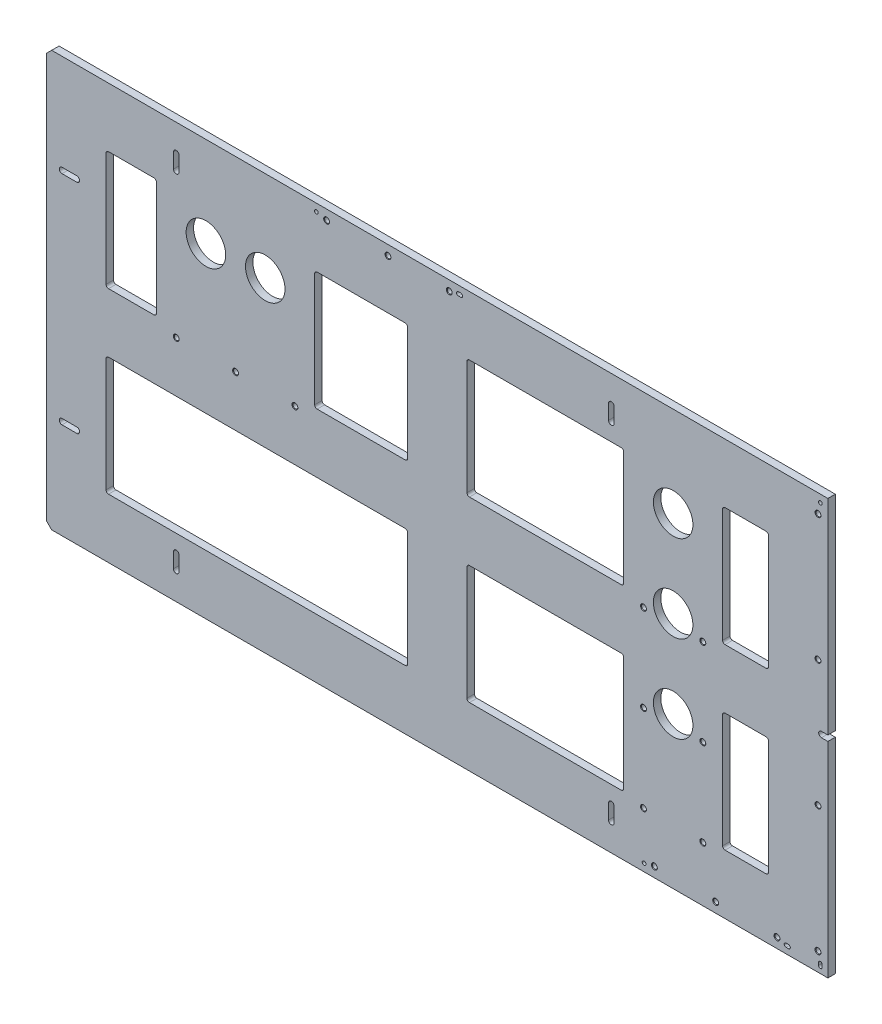
SolidWorks part; units mm, degrees
material "6061-T6 Al"
ref_plane "Front Plane" through (0, 0, 0) normal (0, 0, 1) x (1, 0, 0)
ref_plane "Top Plane" through (0, 0, 0) normal (0, 1, 0) x (1, 0, 0)
ref_plane "Right Plane" through (0, 0, 0) normal (1, 0, 0) x (0, 0, -1)
sketch "Sketch6" plane through (0, 0, 0) normal (0, 0, 1) x (1, 0, 0)
  line L0 (-1.27, -385.7625) -> (-1.27, -122.6312)
  line L1 (-13.0937, -119.0625) -> (-4.8387, -119.0625) construction
  line L2 (-80.645, -309.5625) -> (-80.645, -385.7625) construction
  line L3 (-928.37, -306.3875) -> (-1004.57, -306.3875) construction
  line L4 (0, 498.475) -> (0, -498.475) construction
  line L5 (-998.22, 147.6375) -> (-1.27, 147.6375)
  line L6 (-200, -79.8576) -> (-200, -135.6614) construction
  line L7 (-1004.57, -379.4125) -> (-1004.57, 141.2875)
  line L8 (-1.27, -385.7625) -> (-998.22, -385.7625)
  line L9 (-200, -135.6614) -> (-200, -191.4652) construction
  line L13 (-1004.57, -119.0625) -> (-483.87, -119.0625) construction
  line L15 (-1.27, -385.7625) -> (1.27, -385.7625) construction
  line L36 (-834.6313, 112.7125) -> (-834.6313, 93.6625)
  line L37 (-841.7687, 112.7125) -> (-841.7687, 93.6625)
  line L38 (-275.8313, 112.7125) -> (-275.8313, 93.6625)
  line L39 (-282.9687, 93.6625) -> (-282.9687, 112.7125)
  line L40 (-282.9687, -331.7875) -> (-282.9687, -350.8375)
  line L41 (-275.8313, -350.8375) -> (-275.8313, -331.7875)
  line L42 (-841.7687, -350.8375) -> (-841.7687, -331.7875)
  line L43 (-834.6313, -350.8375) -> (-834.6313, -331.7875)
  line L44 (-838.2, 112.7125) -> (-838.2, 103.1875) construction
  line L45 (-838.2, 103.1875) -> (-838.2, 93.6625) construction
  line L46 (-838.2, -350.8375) -> (-838.2, -341.3125) construction
  line L47 (-838.2, -341.3125) -> (-838.2, -331.7875) construction
  line L48 (-984.885, -255.1938) -> (-965.835, -255.1938)
  line L49 (-984.885, -262.3312) -> (-965.835, -262.3312)
  line L50 (-984.885, 24.2062) -> (-965.835, 24.2062)
  line L51 (-984.885, 17.0688) -> (-965.835, 17.0688)
  line L60 (-1004.57, 141.2875) -> (-998.22, 147.6375)
  line L61 (-998.22, -385.7625) -> (-1004.57, -379.4125)
  line L66 (-984.885, -255.1938) -> (-975.36, -258.7625) construction
  line L67 (-975.36, -258.7625) -> (-965.835, -262.3312) construction
  line L68 (-200, -79.8576) -> (-200, -24.0538) construction
  line L70 (-133.325, 71.4375) -> (-80.645, 71.4375)
  line L71 (-136.5, 68.2625) -> (-136.5, -77.7875)
  line L72 (-133.325, -309.5625) -> (-80.645, -309.5625)
  line L74 (-77.47, 68.2625) -> (-77.47, -77.7875)
  line L75 (-80.645, 71.4375) -> (-80.645, 147.6375) construction
  line L76 (-263.5, 68.2625) -> (-263.5, -77.7875)
  line L77 (-136.5, -160.3375) -> (-136.5, -306.3875)
  line L78 (-263.5, -160.3375) -> (-263.5, -306.3875)
  line L79 (-1.27, 147.6375) -> (-1004.57, -385.7625) construction
  line L80 (-502.92, 68.2625) -> (-502.92, -119.0625) construction
  line L81 (-266.675, 71.4375) -> (-461.645, 71.4375)
  line L82 (-660.4, 68.2625) -> (-660.4, -77.7875)
  line L83 (-266.675, -157.1625) -> (-461.645, -157.1625)
  line L86 (-657.225, -80.9625) -> (-544.195, -80.9625)
  line L87 (-266.675, -309.5625) -> (-461.645, -309.5625)
  line L88 (-464.82, 68.2625) -> (-464.82, -77.7875)
  line L89 (-464.82, -160.3375) -> (-464.82, -306.3875)
  line L90 (-928.37, -160.3375) -> (-928.37, -306.3875)
  line L91 (-77.47, 68.2625) -> (-1.27, 68.2625) construction
  line L92 (-541.02, -160.3375) -> (-541.02, -306.3875)
  line L93 (-541.02, 68.2625) -> (-541.02, -77.7875)
  line L94 (-544.195, 71.4375) -> (-657.225, 71.4375)
  line L95 (-461.645, -80.9625) -> (-266.675, -80.9625)
  line L96 (-544.195, -157.1625) -> (-925.195, -157.1625)
  line L97 (-544.195, -309.5625) -> (-925.195, -309.5625)
  line L98 (-541.02, 68.2625) -> (-464.82, 68.2625) construction
  line L165 (-800.1, 31.75) -> (-723.9, 31.75) construction
  line L166 (-762, 31.75) -> (-762, -80.9625) construction
  line L168 (-925.195, 71.4375) -> (-866.775, 71.4375)
  line L169 (-928.37, 68.2625) -> (-928.37, -77.7875)
  line L170 (-925.195, -80.9625) -> (-866.775, -80.9625)
  line L171 (-863.6, 68.2625) -> (-863.6, -77.7875)
  line L178 (-502.92, -119.0625) -> (-502.92, -385.7625) construction
  line L180 (-133.325, -80.9625) -> (-80.645, -80.9625)
  line L181 (-133.325, -157.1625) -> (-80.645, -157.1625)
  line L182 (-77.47, -160.3375) -> (-77.47, -306.3875)
  line L186 (-200, -24.0538) -> (-200, 31.75) construction
  line L187 (-241.275, -223.2152) -> (-158.725, -223.2152) construction
  line L188 (-244.45, -226.3902) -> (-244.45, -306.3875) construction
  line L189 (-241.275, -309.5625) -> (-158.725, -309.5625) construction
  line L190 (-155.55, -226.3902) -> (-155.55, -306.3875) construction
  line L191 (-155.55, -24.0538) -> (-155.55, -44.9326) construction
  line L195 (-241.275, 0) -> (-158.725, 0) construction
  line L196 (-244.45, -3.175) -> (-244.45, -44.9326) construction
  line L197 (-241.275, -48.1076) -> (-158.725, -48.1076) construction
  line L198 (-155.55, -3.175) -> (-155.55, -24.0538) construction
  line L206 (-841.375, 0) -> (-790.575, 0) construction
  line L207 (-844.55, -3.175) -> (-844.55, -77.7875) construction
  line L208 (-841.375, -80.9625) -> (-790.575, -80.9625) construction
  line L209 (-787.4, -3.175) -> (-787.4, -77.7875) construction
  line L210 (-736.6, -3.175) -> (-736.6, -77.7875) construction
  line L211 (-682.625, -80.9625) -> (-733.425, -80.9625) construction
  line L212 (-679.45, -3.175) -> (-679.45, -77.7875) construction
  line L214 (-682.625, 0) -> (-733.425, 0) construction
  line L228 (-1.27, -122.6312) -> (-9.525, -122.6312)
  line L229 (-1.27, -115.4938) -> (-9.525, -115.4938)
  line L230 (-1.27, -115.4938) -> (-1.27, 147.6375)
  circle A5 centre (-723.9, 31.75) radius 25.4
  circle A6 centre (-800.1, 31.75) radius 25.4
  circle A10 centre (-200, -191.4652) radius 25.4
  circle A11 centre (-200, -79.8576) radius 25.4
  circle A12 centre (-200, 31.75) radius 25.4
  arc A17 (-834.6313, 93.6625) -> (-841.7687, 93.6625) centre (-838.2, 93.6625) cw
  arc A18 (-841.7687, 112.7125) -> (-834.6313, 112.7125) centre (-838.2, 112.7125) cw
  arc A19 (-275.8313, 93.6625) -> (-282.9687, 93.6625) centre (-279.4, 93.6625) cw
  arc A20 (-275.8313, 112.7125) -> (-282.9687, 112.7125) centre (-279.4, 112.7125) ccw
  arc A21 (-275.8313, -350.8375) -> (-282.9687, -350.8375) centre (-279.4, -350.8375) cw
  arc A22 (-275.8313, -331.7875) -> (-282.9687, -331.7875) centre (-279.4, -331.7875) ccw
  arc A23 (-841.7687, -350.8375) -> (-834.6313, -350.8375) centre (-838.2, -350.8375) ccw
  arc A24 (-834.6313, -331.7875) -> (-841.7687, -331.7875) centre (-838.2, -331.7875) ccw
  arc A25 (-984.885, -262.3312) -> (-984.885, -255.1938) centre (-984.885, -258.7625) cw
  arc A26 (-965.835, -255.1938) -> (-965.835, -262.3312) centre (-965.835, -258.7625) cw
  arc A31 (-965.835, 17.0688) -> (-965.835, 24.2062) centre (-965.835, 20.6375) ccw
  arc A32 (-984.885, 24.2062) -> (-984.885, 17.0688) centre (-984.885, 20.6375) ccw
  arc A41 (-925.195, -157.1625) -> (-928.37, -160.3375) centre (-925.195, -160.3375) ccw
  arc A42 (-928.37, -306.3875) -> (-925.195, -309.5625) centre (-925.195, -306.3875) ccw
  arc A43 (-541.02, -306.3875) -> (-544.195, -309.5625) centre (-544.195, -306.3875) cw
  arc A44 (-541.02, -160.3375) -> (-544.195, -157.1625) centre (-544.195, -160.3375) ccw
  arc A45 (-657.225, 71.4375) -> (-660.4, 68.2625) centre (-657.225, 68.2625) ccw
  arc A46 (-657.225, -80.9625) -> (-660.4, -77.7875) centre (-657.225, -77.7875) cw
  arc A47 (-541.02, -77.7875) -> (-544.195, -80.9625) centre (-544.195, -77.7875) cw
  arc A48 (-541.02, 68.2625) -> (-544.195, 71.4375) centre (-544.195, 68.2625) ccw
  arc A49 (-263.5, 68.2625) -> (-266.675, 71.4375) centre (-266.675, 68.2625) ccw
  arc A50 (-464.82, 68.2625) -> (-461.645, 71.4375) centre (-461.645, 68.2625) cw
  arc A51 (-464.82, -77.7875) -> (-461.645, -80.9625) centre (-461.645, -77.7875) ccw
  arc A52 (-263.5, -77.7875) -> (-266.675, -80.9625) centre (-266.675, -77.7875) cw
  arc A53 (-266.675, -157.1625) -> (-263.5, -160.3375) centre (-266.675, -160.3375) cw
  arc A54 (-464.82, -160.3375) -> (-461.645, -157.1625) centre (-461.645, -160.3375) cw
  arc A55 (-461.645, -309.5625) -> (-464.82, -306.3875) centre (-461.645, -306.3875) cw
  arc A56 (-266.675, -309.5625) -> (-263.5, -306.3875) centre (-266.675, -306.3875) ccw
  arc A57 (-136.5, -306.3875) -> (-133.325, -309.5625) centre (-133.325, -306.3875) ccw
  arc A58 (-80.645, -309.5625) -> (-77.47, -306.3875) centre (-80.645, -306.3875) ccw
  arc A59 (-80.645, 71.4375) -> (-77.47, 68.2625) centre (-80.645, 68.2625) cw
  arc A60 (-133.325, 71.4375) -> (-136.5, 68.2625) centre (-133.325, 68.2625) ccw
  arc A81 (-866.775, -80.9625) -> (-863.6, -77.7875) centre (-866.775, -77.7875) ccw
  arc A93 (-928.37, -77.7875) -> (-925.195, -80.9625) centre (-925.195, -77.7875) ccw
  arc A95 (-866.775, 71.4375) -> (-863.6, 68.2625) centre (-866.775, 68.2625) cw
  arc A96 (-925.195, 71.4375) -> (-928.37, 68.2625) centre (-925.195, 68.2625) ccw
  arc A101 (-133.325, -157.1625) -> (-136.5, -160.3375) centre (-133.325, -160.3375) ccw
  arc A102 (-80.645, -157.1625) -> (-77.47, -160.3375) centre (-80.645, -160.3375) cw
  arc A103 (-80.645, -80.9625) -> (-77.47, -77.7875) centre (-80.645, -77.7875) ccw
  arc A104 (-136.5, -77.7875) -> (-133.325, -80.9625) centre (-133.325, -77.7875) ccw
  arc A109 (-158.725, -48.1076) -> (-155.55, -44.9326) centre (-158.725, -44.9326) ccw construction
  arc A110 (-158.725, 0) -> (-155.55, -3.175) centre (-158.725, -3.175) cw construction
  arc A111 (-241.275, 0) -> (-244.45, -3.175) centre (-241.275, -3.175) ccw construction
  arc A112 (-244.45, -44.9326) -> (-241.275, -48.1076) centre (-241.275, -44.9326) ccw construction
  arc A117 (-158.725, -309.5625) -> (-155.55, -306.3875) centre (-158.725, -306.3875) ccw construction
  arc A118 (-158.725, -223.2152) -> (-155.55, -226.3902) centre (-158.725, -226.3902) cw construction
  arc A119 (-241.275, -223.2152) -> (-244.45, -226.3902) centre (-241.275, -226.3902) ccw construction
  arc A120 (-244.45, -306.3875) -> (-241.275, -309.5625) centre (-241.275, -306.3875) ccw construction
  arc A125 (-679.45, -77.7875) -> (-682.625, -80.9625) centre (-682.625, -77.7875) cw construction
  arc A126 (-682.625, 0) -> (-679.45, -3.175) centre (-682.625, -3.175) cw construction
  arc A127 (-733.425, 0) -> (-736.6, -3.175) centre (-733.425, -3.175) ccw construction
  arc A128 (-733.425, -80.9625) -> (-736.6, -77.7875) centre (-733.425, -77.7875) cw construction
  arc A129 (-790.575, -80.9625) -> (-787.4, -77.7875) centre (-790.575, -77.7875) ccw construction
  arc A130 (-790.575, 0) -> (-787.4, -3.175) centre (-790.575, -3.175) cw construction
  arc A131 (-841.375, 0) -> (-844.55, -3.175) centre (-841.375, -3.175) ccw construction
  arc A132 (-844.55, -77.7875) -> (-841.375, -80.9625) centre (-841.375, -77.7875) ccw construction
  arc A141 (-9.525, -122.6312) -> (-9.525, -115.4938) centre (-9.525, -119.0625) cw
  dimension "D2" = 533.4
  dimension "D5" = 147.6375
  dimension "D6" = 203.2
  dimension "D7" = 2.54
  dimension "D9" = 9.525
  dimension "D12" = 975.36
  dimension "D11" = 3.175
  dimension "D13" = 200
  dimension "D14" = 50.8
  dimension "D16" = 223.2152
  dimension "D19" = 7.1374
  dimension "D20" = 444.5
  dimension "D22" = 558.8
  dimension "D23" = 279.4
  dimension "D21" = 279.4
  dimension "D34" = 63.5
  dimension "D17" = 31.75
  dimension "D44" = 88.9
  dimension "D49" = 19.05
  dimension "D47" = 63.5
  dimension "D8" = 1004.57
  dimension "D15" = 762
  dimension "D18" = 19.05
  dimension "D29" = 76.2
  dimension "D30" = 127
  dimension "D33" = 76.2
  dimension "D45" = 6.35
  dimension "D46" = 6.35
  dimension "D48" = 6.35
extrude "Boss-Extrude1" add sketch "Sketch6" against normal mid plane 9.525
hole_wizard "1/4-20 Tapped Hole1" positions "Sketch8" profile "Sketch7" tap size "1/4-20" standard "ANSI Inch" end condition through all
sketch "Sketch8" plane through (0, 0, 4.7625) normal (0, 0, 1) x (1, 0, 0)
  line L0 (-762, -92.075) -> (-723.9, 31.75) construction
  line L1 (-762, -92.075) -> (-800.1, 31.75) construction
  line L2 (-762, -92.075) -> (-800.1, -92.075) construction
  line L3 (-762, -92.075) -> (-723.9, -92.075) construction
  line L6 (-238.1, -92.075) -> (-238.1, -203.6826) construction
  line L7 (-238.1, -203.6826) -> (-238.1, -315.2902) construction
  line L10 (-238.1, -92.075) -> (-200, -92.075) construction
  line L11 (-200, -79.8576) -> (-200, 31.75) construction
  line L12 (-200, -92.075) -> (-161.9, -92.075) construction
  line L13 (-238.1, -203.6826) -> (-200, -203.6826) construction
  line L14 (-238.1, -315.2902) -> (-200, -315.2902) construction
  line L15 (-200, -203.6826) -> (-161.9, -203.6826) construction
  line L16 (-200, -315.2902) -> (-161.9, -315.2902) construction
  line L17 (-800.1, -92.075) -> (-838.2, -92.075) construction
  line L18 (-723.9, -92.075) -> (-685.8, -92.075) construction
  line L39 (-838.2, -92.075) -> (-838.2, 31.75) construction
  circle A4 centre (-200, 31.75) radius 25.4 construction
  circle A5 centre (-200, -79.8576) radius 25.4 construction
  point P0 (-762, -92.075)
  point P2 (-685.8, -92.075)
  point P4 (-838.2, -92.075)
  point P33 (-238.1, -92.075)
  point P35 (-238.1, -203.6826)
  point P37 (-238.1, -315.2902)
  point P45 (-161.9, -315.2902)
  point P46 (-161.9, -203.6826)
  point P47 (-161.9, -92.075)
  dimension "D1" = 123.825
  dimension "D2" = 152.4
  dimension "D4" = 76.2
sketch "Sketch7" plane through (-762, -92.075, 4.7625) normal (1, 0, 0) x (0, -1, 0)
  line L0 (0, 0) -> (0, 9.525)
  line L1 (0, 9.525) -> (3.81, 9.525)
  line L2 (3.175, 8.89) -> (3.175, 0.635)
  line L3 (3.175, 0.635) -> (3.81, 0)
  line L5 (3.81, 0) -> (0, 0)
  line L6 (-3.175, 0.635) -> (-3.81, 0) construction
  line L7 (3.81, 9.525) -> (3.175, 8.89)
  line L8 (-3.81, 9.525) -> (-3.175, 8.89) construction
  line L11 (0, -6.35) -> (0, 107.95) construction
  dimension "Thread Major Dia." = 6.35
  dimension "Thru Tap Drill Depth" = 9.525
  dimension "Near C'Sink Dia." = 7.62
  dimension "Near C'Sink Angle" = 90
  dimension "Far C'Sink Dia." = 7.62
  dimension "Far C'Sink Angle" = 90
hole_wizard "3/16 (0.1875) Diameter Hole1" positions "Sketch10" profile "Sketch9" hole size "3/16" standard "ANSI Inch" end condition through all
sketch "Sketch10" plane through (650.0872, -13.9256, 4.7625) normal (0, 0, 1) x (1, 0, 0)
  line L16 (-651.3572, 161.5631) -> (-1648.3072, 161.5631) construction
  line L18 (-661.0092, 151.9111) -> (-661.0092, 161.5631) construction
  line L19 (-661.0092, 151.9111) -> (-651.3572, 151.9111) construction
  line L20 (-651.3572, -101.5682) -> (-651.3572, 161.5631) construction
  line L21 (-661.0092, -362.1849) -> (-661.0092, -371.8369) construction
  line L22 (-1648.3072, -371.8369) -> (-651.3572, -371.8369) construction
  line L23 (-1125.9304, 151.9111) -> (-1122.8824, 151.9111) construction
  line L24 (-1125.9304, 154.2987) -> (-1122.8824, 154.2987) construction
  line L25 (-1125.9304, 149.5235) -> (-1122.8824, 149.5235) construction
  line L29 (-661.0092, -363.7089) -> (-661.0092, -360.6609) construction
  line L30 (-663.3968, -363.7089) -> (-663.3968, -360.6609) construction
  line L31 (-658.6216, -363.7089) -> (-658.6216, -360.6609) construction
  line L37 (-705.0532, -362.1849) -> (-702.0052, -362.1849) construction
  line L38 (-705.0532, -359.7973) -> (-702.0052, -359.7973) construction
  line L39 (-705.0532, -364.5725) -> (-702.0052, -364.5725) construction
  line L43 (-1124.4064, 151.9111) -> (-1308.3024, 151.9111) construction
  line L45 (-703.5292, -362.185) -> (-887.4252, -362.185) construction
  line L47 (-651.3572, -371.8369) -> (-651.3572, -108.7056) construction
  arc A0 (-1125.9304, 154.2987) -> (-1125.9304, 149.5235) centre (-1125.9304, 151.9111) ccw construction
  arc A1 (-1122.8824, 149.5235) -> (-1122.8824, 154.2987) centre (-1122.8824, 151.9111) ccw construction
  arc A4 (-663.3968, -363.7089) -> (-658.6216, -363.7089) centre (-661.0092, -363.7089) ccw construction
  arc A5 (-658.6216, -360.6609) -> (-663.3968, -360.6609) centre (-661.0092, -360.6609) ccw construction
  arc A6 (-705.0532, -359.7973) -> (-705.0532, -364.5725) centre (-705.0532, -362.1849) ccw construction
  arc A7 (-702.0052, -364.5725) -> (-702.0052, -359.7973) centre (-702.0052, -362.1849) ccw construction
  point P36 (-1308.3024, 151.9111)
  point P40 (-661.0092, 151.9111)
  point P136 (-887.4252, -362.1849)
  dimension "D4" = 4.7752
  dimension "D1" = 9.652
  dimension "D2" = 656.9452
  dimension "D3" = 183.896
  dimension "D5" = 3.048
  dimension "D6" = 236.068
sketch "Sketch9" plane through (-658.2152, 137.9855, 4.7625) normal (1, 0, 0) x (0, -1, 0)
  line L0 (0, 0) -> (0, 9.525)
  line L1 (0, 9.525) -> (2.3876, 9.525)
  line L2 (2.3876, 9.525) -> (2.3876, 0)
  line L5 (2.3876, 0) -> (0, 0)
  line L11 (0, -6.35) -> (0, 107.95) construction
  dimension "Thru Hole Dia." = 4.7752
  dimension "Thru Hole Depth" = 9.525
sketch "Sketch13" plane through (0, 0, 4.7625) normal (0, 0, 1) x (1, 0, 0)
  line L0 (-475.8432, 137.9855) -> (-472.7952, 137.9855) construction
  line L1 (-475.8432, 140.3731) -> (-472.7952, 140.3731)
  line L2 (-475.8432, 135.5979) -> (-472.7952, 135.5979)
  line L6 (-10.922, -374.5865) -> (-10.922, -377.6345) construction
  line L7 (-8.5344, -374.5865) -> (-8.5344, -377.6345)
  line L8 (-13.3096, -374.5865) -> (-13.3096, -377.6345)
  line L9 (-475.8432, 135.5979) -> (-472.7952, 135.5979) construction
  line L10 (-54.966, -376.1105) -> (-51.918, -376.1105) construction
  line L11 (-54.966, -373.7229) -> (-51.918, -373.7229)
  line L12 (-54.966, -378.4981) -> (-51.918, -378.4981)
  line L13 (-54.966, -378.4981) -> (-51.918, -378.4981) construction
  line L16 (-54.966, -376.1105) -> (-51.918, -376.1105) construction
  arc A0 (-475.8432, 140.3731) -> (-475.8432, 135.5979) centre (-475.8432, 137.9855) ccw
  arc A1 (-472.7952, 135.5979) -> (-472.7952, 140.3731) centre (-472.7952, 137.9855) ccw
  arc A4 (-8.5344, -374.5865) -> (-13.3096, -374.5865) centre (-10.922, -374.5865) ccw
  arc A5 (-13.3096, -377.6345) -> (-8.5344, -377.6345) centre (-10.922, -377.6345) ccw
  arc A6 (-472.7952, 135.5979) -> (-472.7952, 140.3731) centre (-472.7952, 137.9855) ccw construction
  arc A7 (-54.966, -373.7229) -> (-54.966, -378.4981) centre (-54.966, -376.1105) ccw
  arc A8 (-51.918, -378.4981) -> (-51.918, -373.7229) centre (-51.918, -376.1105) ccw
  arc A11 (-51.918, -378.4981) -> (-51.918, -373.7229) centre (-51.918, -376.1105) ccw construction
  point P2 (-474.3192, 137.9855)
  point P14 (-10.922, -376.1105)
  point P31 (-53.442, -376.1105)
extrude "Cut-Extrude1" cut sketch "Sketch13" against normal through all
hole_wizard "1/4-20 Tapped Hole2" positions "Sketch12" profile "Sketch11" tap size "1/4-20" standard "ANSI Inch" end condition through all
sketch "Sketch12" plane through (0, 0, 4.7625) normal (0, 0, 1) x (1, 0, 0)
  line L0 (-13.97, 124.0155) -> (-13.97, -38.0365) construction
  line L1 (-13.97, -38.0365) -> (-13.97, -200.0885) construction
  line L2 (-13.97, -200.0885) -> (-13.97, -362.1405) construction
  line L3 (-10.922, 137.9855) -> (-13.97, 124.0155) construction
  line L4 (-13.97, -362.1405) -> (-10.922, -376.1105) construction
  line L7 (-224.13, -373.0625) -> (-237.338, -376.1105) construction
  line L8 (-474.3192, 137.9855) -> (-487.5272, 134.9375) construction
  line L9 (-487.5272, 134.9375) -> (-645.0072, 134.9375) construction
  line L11 (-645.0072, 134.9375) -> (-658.2152, 137.9855) construction
  line L14 (-1.27, 147.6375) -> (-998.22, 147.6375) construction
  line L15 (-224.13, -373.0625) -> (-66.65, -373.0625) construction
  line L16 (-66.65, -373.0625) -> (-53.442, -376.1105) construction
  line L17 (-1.27, -115.4938) -> (-1.27, 147.6375) construction
  point P0 (-13.97, 124.0155)
  point P1 (-13.97, -38.0365)
  point P4 (-13.97, -200.0885)
  point P7 (-13.97, -362.1405)
  point P58 (-66.65, -373.0625)
  point P60 (-145.39, -373.0625)
  point P62 (-224.13, -373.0625)
  point P81 (-566.2672, 134.9375)
  point P83 (-487.5272, 134.9375)
  point P85 (-645.0072, 134.9375)
  dimension "D1" = 14.2986
  dimension "D2" = 12.7
  dimension "D3" = 157.48
  dimension "D4" = 486.156
  dimension "D5" = 12.7
sketch "Sketch11" plane through (-13.97, 124.0155, 4.7625) normal (1, 0, 0) x (0, -1, 0)
  line L0 (0, 0) -> (0, 9.525)
  line L1 (0, 9.525) -> (3.81, 9.525)
  line L2 (3.175, 8.89) -> (3.175, 0.635)
  line L3 (3.175, 0.635) -> (3.81, 0)
  line L5 (3.81, 0) -> (0, 0)
  line L6 (-3.175, 0.635) -> (-3.81, 0) construction
  line L7 (3.81, 9.525) -> (3.175, 8.89)
  line L8 (-3.81, 9.525) -> (-3.175, 8.89) construction
  line L11 (0, -6.35) -> (0, 107.95) construction
  dimension "Thread Major Dia." = 6.35
  dimension "Thru Tap Drill Depth" = 9.525
  dimension "Near C'Sink Dia." = 7.62
  dimension "Near C'Sink Angle" = 90
  dimension "Far C'Sink Dia." = 7.62
  dimension "Far C'Sink Angle" = 90
